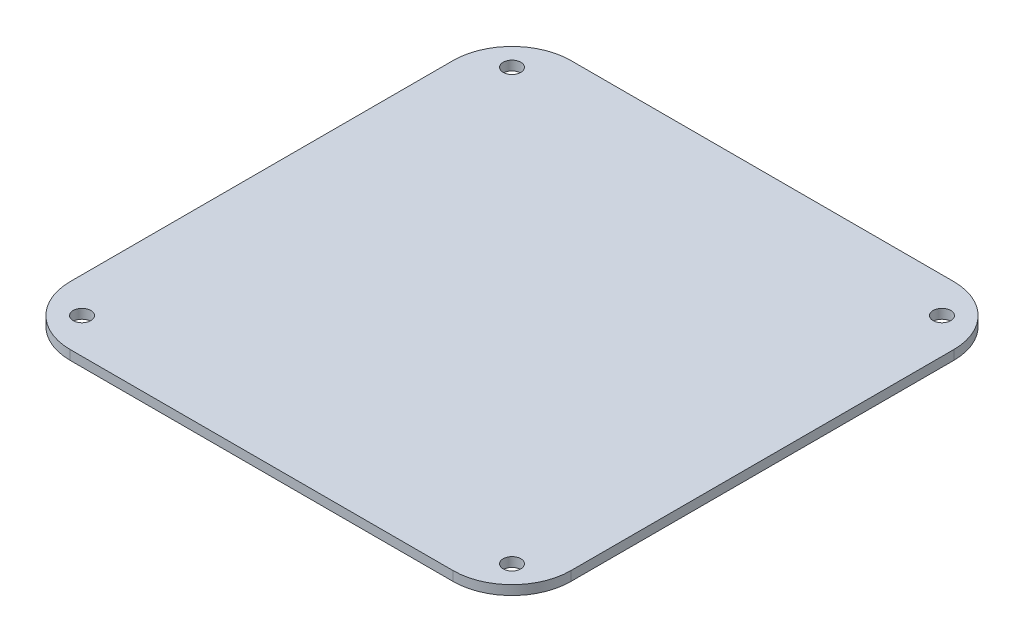
SolidWorks part; units mm, degrees
ref_plane "Front Plane" through (0, 0, 0) normal (0, 0, 1) x (1, 0, 0)
ref_plane "Top Plane" through (0, 0, 0) normal (0, 1, 0) x (1, 0, 0)
ref_plane "Right Plane" through (0, 0, 0) normal (1, 0, 0) x (0, 0, -1)
sketch "Sketch1" plane through (0, 0, 0) normal (0, 1, 0) x (1, 0, 0)
  line L1 (0, 0) -> (85, 0)
  line L2 (0, 0) -> (0, 85)
  line L3 (0, 85) -> (85, 85)
  line L4 (85, 0) -> (85, 85)
  circle A0 centre (6, 79) radius 1.5
  circle A1 centre (6, 6) radius 1.5
  circle A2 centre (79, 6) radius 1.5
  circle A3 centre (79, 79) radius 1.5
  dimension "D3" = 3
  dimension "D4" = 3
  dimension "D5" = 3
  dimension "D6" = 3
  dimension "D7" = 6
  dimension "D8" = 6
  dimension "D9" = 6
  dimension "D10" = 6
  dimension "D11" = 6
  dimension "D12" = 6
  dimension "D13" = 6
  dimension "D1" = 85
  dimension "D2" = 85
  dimension "D14" = 6
extrude "Boss-Extrude1" add sketch "Sketch1" along normal blind 1.6
fillet "Fillet1" radius 10 4 edges at (0, 0.8, -85) (85, 0.8, -85) (85, 0.8, 0) (0, 0.8, 0)
